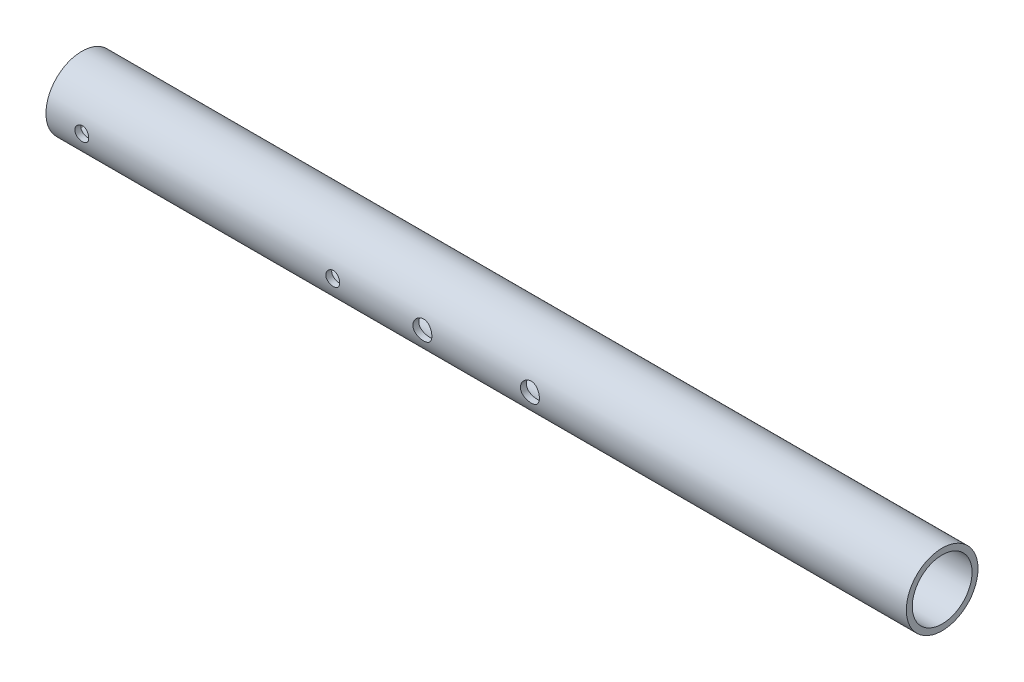
SolidWorks part; units mm, degrees
ref_plane "Front Plane" through (0, 0, 0) normal (0, 0, 1) x (1, 0, 0)
ref_plane "Top Plane" through (0, 0, 0) normal (0, 1, 0) x (1, 0, 0)
ref_plane "Right Plane" through (0, 0, 0) normal (1, 0, 0) x (0, 0, -1)
sketch "Sketch1" plane through (0, 0, 0) normal (1, 0, 0) x (0, 0, -1)
  circle A0 centre (0, 0) radius 12.7
  circle A1 centre (0, 0) radius 10.5918
  dimension "D1" = 25.4
  dimension "D2" = 21.1836
extrude "Boss-Extrude1" add sketch "Sketch1" along normal blind 304.8
sketch "Sketch8" plane through (0, 0, 0) normal (0, 0, 1) x (1, 0, 0)
  line L0 (0, 12.7) -> (0, -12.7) construction
  circle A0 centre (12.7, 0) radius 2.4638
  circle A1 centre (101.6, 0) radius 2.4638
  circle A2 centre (133.35, 0) radius 3.3655
  circle A3 centre (171.45, 0) radius 3.3655
  dimension "D5" = 6.731
  dimension "D6" = 4.9276
  dimension "D1" = 12.7
  dimension "D2" = 88.9
  dimension "D3" = 133.35
  dimension "D4" = 38.1
extrude "Cut-Extrude1" cut sketch "Sketch8" against normal through all both and the other way through all
